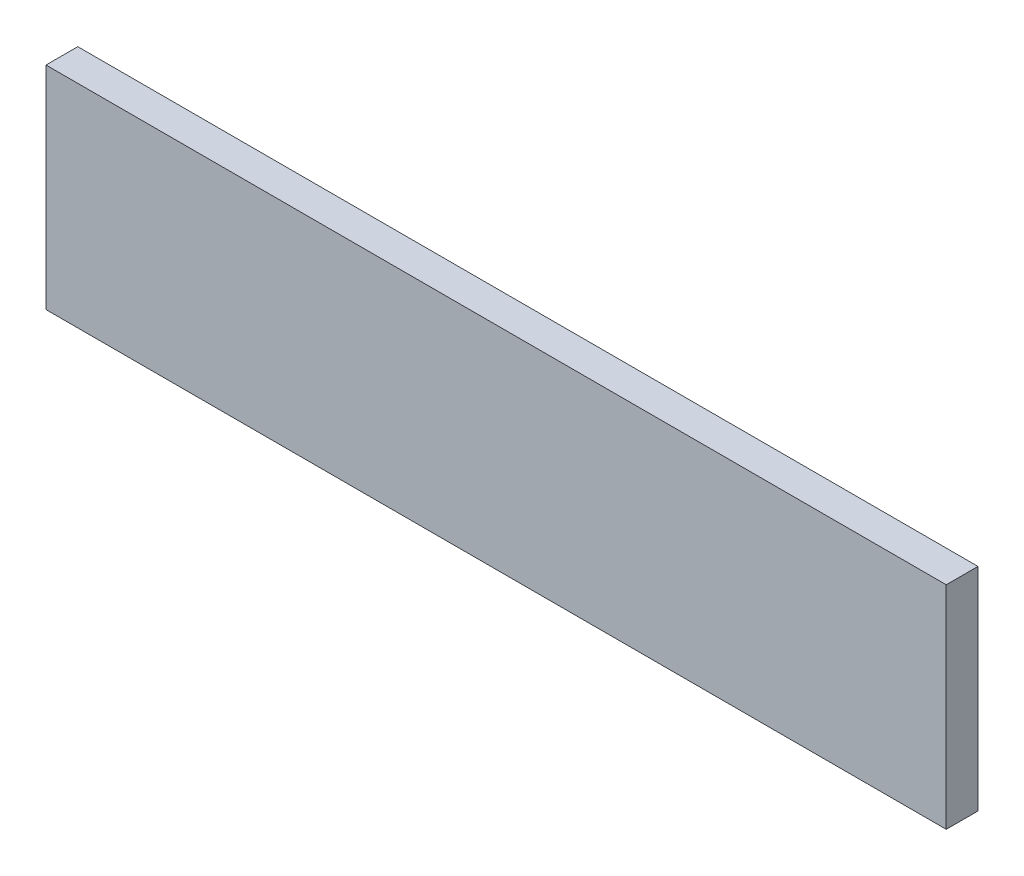
SolidWorks part; units mm, degrees
material " 09Г2С ГОСТ 4543-71"
ref_plane "Спереди" through (0, 0, 0) normal (0, 0, 1) x (1, 0, 0)
ref_plane "Сверху" through (0, 0, 0) normal (0, 1, 0) x (1, 0, 0)
ref_plane "Слева" through (0, 0, 0) normal (1, 0, 0) x (0, 0, -1)
sketch "Эскиз1" plane through (0, 0, 0) normal (0, 0, 1) x (1, 0, 0)
  line L1 (0, 0) -> (170, 0)
  line L2 (0, 0) -> (0, 40)
  line L3 (0, 40) -> (170, 40)
  line L4 (170, 0) -> (170, 40)
  dimension "D1" = 40
  dimension "D2" = 170
extrude "Вытянуть1" add sketch "Эскиз1" along normal blind 6
